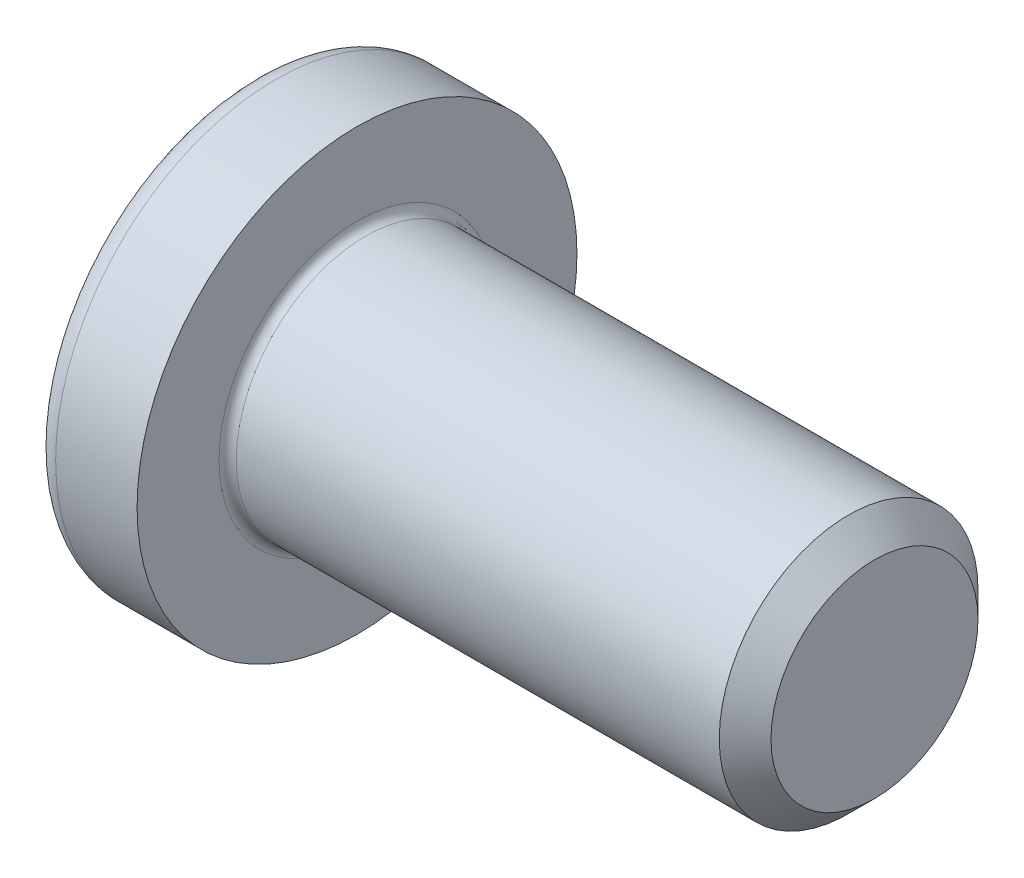
SolidWorks part; units mm, degrees
material "Acier allié"
ref_plane "Plane1" through (0, 0, 0) normal (0, 0, 1) x (1, 0, 0)
ref_plane "Plane2" through (0, 0, 0) normal (0, 1, 0) x (1, 0, 0)
ref_plane "Plane3" through (0, 0, 0) normal (1, 0, 0) x (0, 0, -1)
sketch "BodySke" plane through (0, 0, 0) normal (0, 0, 1) x (1, 0, 0)
  line L0 (1.8, 1.5) -> (1.8, 2.55)
  line L1 (2.05, 6.35) -> (2.05, -3.175) construction
  line L2 (-25.4, 0) -> (127, 0) construction
  line L3 (7.8, 0) -> (0, 0)
  line L4 (1.8, 1.5) -> (7.8, 1.5)
  line L5 (7.8, 1.5) -> (7.8, 0)
  line L6 (0.8558, 2.55) -> (1.8, 2.55)
  line L8 (1.8, 6.35) -> (1.8, -3.175) construction
  arc A0 (0.6192, 2.4101) -> (0, 0) centre (5, 0) ccw
  arc A2 (0.6192, 2.4101) -> (0.8558, 2.55) centre (0.8558, 2.28) cw
  dimension "Head_fillet_rad" = 0.27
  dimension "Head_crown_rad" = 5
  dimension "Head_ht" = 1.8
  dimension "Diameter" = 3
  dimension "Length" = 6
  dimension "Head_dia" = 5.1
  dimension "Advance" = 0.5
  dimension "Thread_nom" = 6
revolve "Base-Revolve" add sketch "BodySke" angle 360 about L2
cosmetic thread "ThreadCosmetic" parameters "Thread_length"=5, "Thread_minor"=2.439
fillet "Fillet1" radius 0.1 1 edges at (1.8, 0, 1.5)
sketch "Sketch3" plane through (0, 0, 0) normal (1, 0, 0) x (0, 0, -1)
  line L0 (0.45, -1.75) -> (-0.45, -1.75)
  line L1 (0.45, -1.75) -> (0.45, 1.75)
  line L2 (-0.45, 1.75) -> (0.45, 1.75)
  line L3 (-0.45, 1.75) -> (-0.45, -1.75)
  dimension "D1" = 1.75
  dimension "Cross_dia" = 3.5
  dimension "D2" = 0.45
  dimension "Cross_width" = 0.9
ref_plane "Plane4" through (1.75, 0, 0) normal (1, 0, 0) x (0, 0, -1)
sketch "Sketch4" plane through (1.75, 0, 0) normal (1, 0, 0) x (0, 0, -1)
  line L0 (0.45, -0.8775) -> (-0.45, -0.8775)
  line L1 (0.45, -0.8775) -> (0.45, 0.8775)
  line L2 (-0.45, 0.8775) -> (0.45, 0.8775)
  line L3 (-0.45, 0.8775) -> (-0.45, -0.8775)
  dimension "D1" = 0.9
  dimension "D2" = 1.755
  dimension "D3" = 0.45
  dimension "D4" = 0.8775
loft "Recess" cut profiles "Sketch3", "Sketch4"
pattern_circular "RecPat" count 2 every 90 about axis through (0, 0, 0) along (1, 0, 0) of "Recess"
sketch "RecCorSke" plane through (0, 0, 0) normal (0, 0, 1) x (1, 0, 0)
  line L0 (-3.175, 0) -> (15.875, 0) construction
  line L1 (-25.4, 0) -> (127, 0) construction
  line L2 (0, 0) -> (0, 0.6784)
  line L3 (0, 0.6784) -> (1.75, 0.556)
  line L4 (1.75, 0.556) -> (1.9307, 0)
  line L5 (1.9307, 0) -> (0, 0)
  dimension "Diameter" = 1.112
  dimension "Depth" = 1.75
  dimension "Draft_angle" = 4
  dimension "Bottom_angle" = 18
revolve "RecessCore" cut sketch "RecCorSke" angle 360 about L0
sketch "ThdSchSke" plane through (0, 0, 0) normal (0, 0, 1) x (1, 0, 0)
  line L0 (2.8, -1.2195) -> (2.6036, -1.5)
  line L1 (2.8, -1.2195) -> (2.9964, -1.5)
  line L2 (2.9964, -1.5) -> (2.9964, -1.875)
  line L3 (-3.175, 0) -> (5.1513, 0) construction
  line L5 (2.9964, -1.875) -> (2.6036, -1.875)
  line L6 (2.6036, -1.875) -> (2.6036, -1.5)
  dimension "Thread_minor" = 2.439
  dimension "Diameter" = 3
  dimension "Start" = 2.8
  dimension "SideAngle" = 55
  dimension "VeeAngle" = 70
  dimension "Overcut" = 3.75
revolve "ThreadSchematic" [suppressed] cut sketch "ThdSchSke" angle 360 about L3
pattern_linear "ThdSchPat" [suppressed]
chamfer "Chanfrein1" distance 0.3 angle 45 1 edges at (7.8, 0, 1.5)
equation "\"D1@Sketch3\" = \"Cross_dia@Sketch3\" / 2"
equation "\"D2@Sketch3\" = \"Cross_width@Sketch3\" / 2"
equation "\"Depth@RecCorSke\" = \"Cross_depth@Plane4\""
equation "\"D1@Sketch4\" = \"Cross_width@Sketch3\""
equation "\"D2@Sketch4\" = \"Cross_dia@Sketch3\" - 2.0 * \"Cross_depth@Plane4\" * tan(26.5  * 0.017453292)"
equation "\"D3@Sketch4\" = \"D1@Sketch4\" / 2"
equation "\"D4@Sketch4\" = \"D2@Sketch4\" / 2"
equation "\"Thread_length@ThreadCosmetic\" = ((sgn( (\"Length@BodySke\" - \"Advance@BodySke\" * 2.0 ) - \"Thread_nom@BodySke\" )-1)*( (\"Length@BodySke\" - \"Advance@BodySke\" * 2.0 ) - \"Thread_nom@BodySke\" ))/-2+ \"Thread_nom@BodySke\""
equation "\"Thread_minor@ThdSchSke\" = \"Thread_minor@ThreadCosmetic\""
equation "\"Diameter@ThdSchSke\" = \"Diameter@BodySke\""
equation "\"Overcut@ThdSchSke\" = \"Diameter@BodySke\" * 1.25"
equation "\"Start@ThdSchSke\" = \"Head_ht@BodySke\" + \"Length@BodySke\" - \"Thread_length@ThreadCosmetic\"  '---Non-countersunk---"
equation "\"Num_threads@ThdSchPat\" = int( \"Thread_length@ThreadCosmetic\" / \"Advance@BodySke\" + 0.999 )  + 1"
equation "\"Advance@ThdSchPat\" = \"Thread_length@ThreadCosmetic\" /  (\"Num_threads@ThdSchPat\" - 1) 'relax it"
